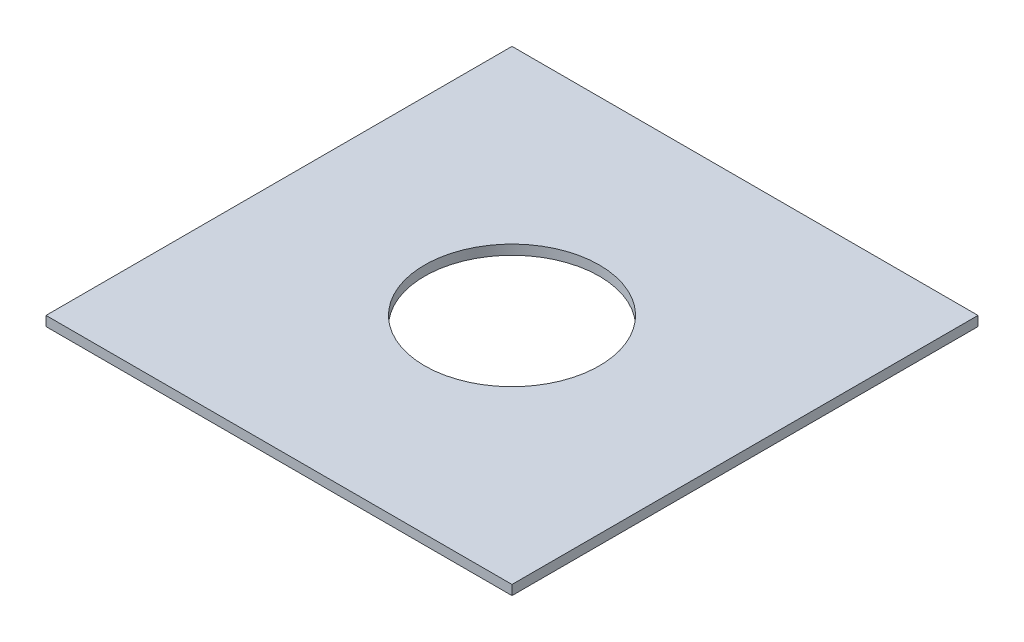
SolidWorks part; units mm, degrees
material "Acrylic (Medium-high impact)"
ref_plane "Front" through (0, 0, 0) normal (0, 0, 1) x (1, 0, 0)
ref_plane "Top" through (0, 0, 0) normal (0, 1, 0) x (1, 0, 0)
ref_plane "Right" through (0, 0, 0) normal (1, 0, 0) x (0, 0, -1)
sketch "Sketch1" plane through (0, 0, 0) normal (0, 1, 0) x (1, 0, 0)
  line L1 (-152.4, 304.8) -> (152.4, 304.8)
  line L2 (-152.4, 304.8) -> (-152.4, 0)
  line L3 (-152.4, 0) -> (152.4, 0)
  line L4 (152.4, 304.8) -> (152.4, 0)
  point P4 (0, 0)
  dimension "D1" = 304.8
  dimension "D2" = 304.8
extrude "Boss-Extrude1" add sketch "Sketch1" along normal blind 6.35
sketch "Sketch2" plane through (0, 6.35, 0) normal (0, 1, 0) x (1, 0, 0)
  line L0 (152.4, 0) -> (152.4, 304.8) construction
  circle A0 centre (0, 152.4) radius 57.15
  point P8 (152.4, 152.4)
  dimension "D1" = 114.3
extrude "Cut-Extrude1" cut sketch "Sketch2" against normal up to next
